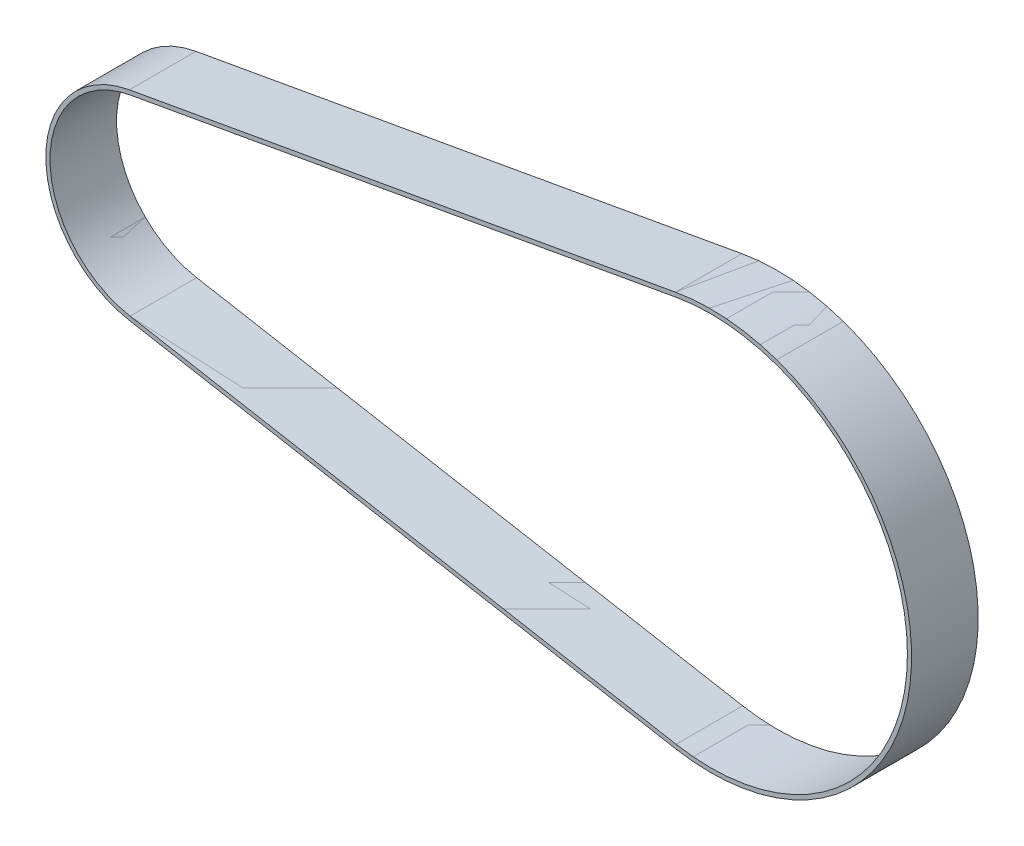
SolidWorks part; units mm, degrees
ref_plane "Front Plane" through (0, 0, 0) normal (0, 0, 1) x (1, 0, 0)
ref_plane "Top Plane" through (0, 0, 0) normal (0, 1, 0) x (1, 0, 0)
ref_plane "Right Plane" through (0, 0, 0) normal (1, 0, 0) x (0, 0, -1)
ref_plane "Plane1" through (0, 0, -8) normal (0, 0, -1) x (-1, 0, 0)
sketch "Sketch1" plane through (0, 0, -8) normal (0, 0, -1) x (-1, 0, 0)
  line L0 (8.5073, -47.4905) -> (139.6874, -23.9913)
  line L1 (139.6874, 23.9913) -> (8.5073, 47.4905)
  line L2 (8.331, 46.5062) -> (139.5111, 23.007)
  line L3 (139.5111, -23.007) -> (8.331, -46.5062)
  arc A0 (8.5073, 47.4905) -> (8.5073, -47.4905) centre (0, 0) ccw
  arc A1 (139.6874, -23.9913) -> (139.6874, 23.9913) centre (135.3897, 0) ccw
  arc A2 (139.5111, 23.007) -> (139.5111, -23.007) centre (135.3897, 0) cw
  arc A3 (8.331, -46.5062) -> (8.331, 46.5062) centre (0, 0) cw
extrude "Boss-Extrude1" add sketch "Sketch1" against normal blind 16
surface "Surface-Knit1"
surface "Surface-Knit2"
